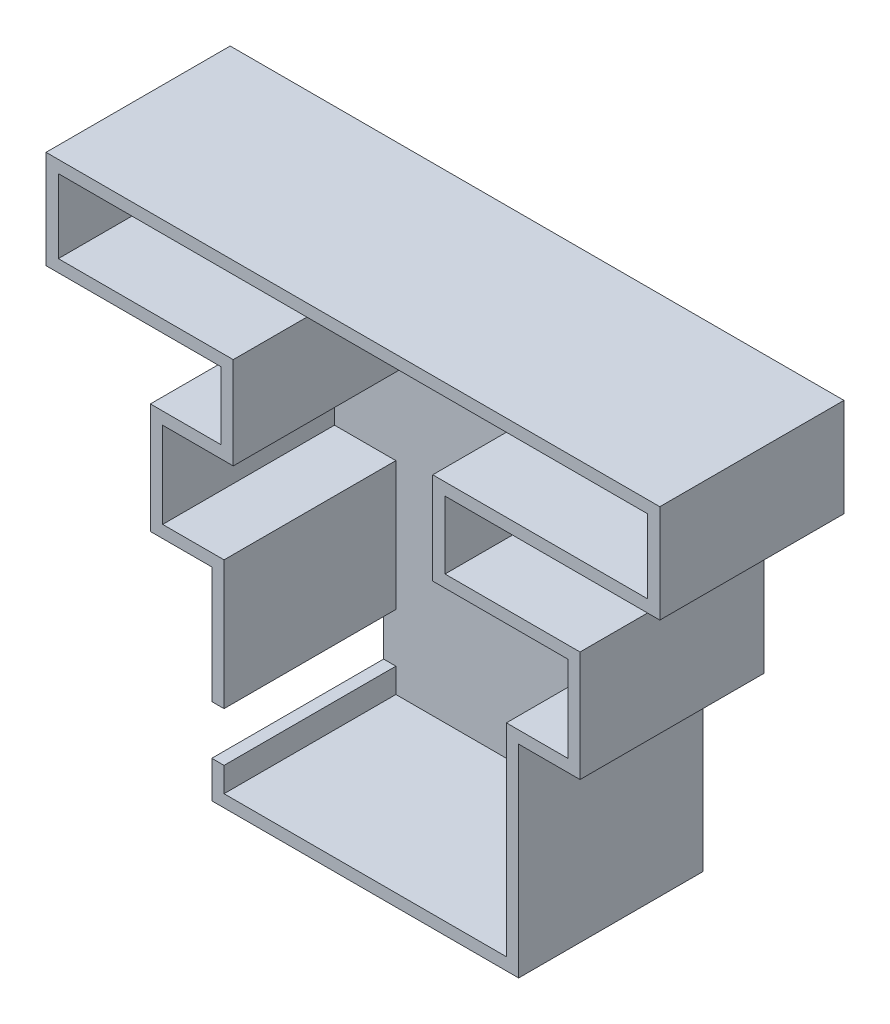
SolidWorks part; units mm, degrees
ref_plane "前视基准面" through (0, 0, 0) normal (0, 0, 1) x (1, 0, 0)
ref_plane "上视基准面" through (0, 0, 0) normal (0, 1, 0) x (1, 0, 0)
ref_plane "右视基准面" through (0, 0, 0) normal (1, 0, 0) x (0, 0, -1)
other "Configuration Table"
sketch "草图3" plane through (0, 0, 0) normal (0, 0, 1) x (1, 0, 0)
  line L0 (-4.5, 23.1299) -> (-4.5, -48.8588) construction
  line L1 (-11.5, 0) -> (11.5, 0)
  line L2 (-11.5, 0) -> (-11.5, -16.5)
  line L3 (-11.5, -16.5) -> (11.5, -16.5)
  line L4 (11.5, 0) -> (11.5, -16.5)
  line L5 (-16.5, 7) -> (16.5, 7)
  line L6 (-16.5, 7) -> (-16.5, 0)
  line L7 (-16.5, 0) -> (16.5, 0)
  line L8 (16.5, 7) -> (16.5, 0)
  line L9 (-10.75, 14.5) -> (5.5, 14.5)
  line L10 (-10.75, 14.5) -> (-10.75, 7)
  line L11 (-10.75, 7) -> (5.5, 7)
  line L12 (5.5, 14.5) -> (5.5, 7)
  line L13 (-26, 21.5) -> (24, 21.5)
  line L14 (-25, 20.5) -> (23, 20.5)
  line L15 (-25, 20.5) -> (-25, 14.5)
  line L16 (-25, 14.5) -> (23, 14.5)
  line L17 (23, 20.5) -> (23, 14.5)
  line L18 (24, 21.5) -> (24, 13.5)
  line L19 (-26, 13.5) -> (-11.75, 13.5)
  line L20 (-26, 21.5) -> (-26, 13.5)
  line L21 (-11.75, 13.5) -> (-11.75, 8)
  line L23 (6.5, 13.5) -> (6.5, 8)
  line L25 (-17.5, 8) -> (-11.75, 8)
  line L26 (17.5, 8) -> (17.5, -1)
  line L27 (-17.5, -1) -> (-12.5, -1)
  line L28 (-17.5, 8) -> (-17.5, -1)
  line L29 (12.5, -1) -> (12.5, -17.5)
  line L30 (-12.5, -17.5) -> (12.5, -17.5)
  line L31 (-12.5, -1) -> (-12.5, -17.5)
  line L33 (-11.75, 15.5) -> (6.5, 15.5) construction
  line L34 (6.5, 15.5) -> (6.5, 6) construction
  line L35 (-11.75, 15.5) -> (-11.75, 6) construction
  line L36 (6.5, 13.5) -> (24, 13.5)
  line L37 (-26, 13.5) -> (24, 13.5) construction
  line L38 (-12.5, 1) -> (12.5, 1) construction
  line L39 (6.5, 8) -> (17.5, 8)
  line L40 (-17.5, 8) -> (17.5, 8) construction
  line L41 (-11.75, 6) -> (6.5, 6) construction
  line L42 (-11.5, 0) -> (11.5, 0) construction
  line L43 (12.5, -1) -> (17.5, -1)
  line L44 (-17.5, -1) -> (17.5, -1) construction
  line L45 (12.5, 1) -> (12.5, -17.5) construction
  line L46 (-12.5, 1) -> (-12.5, -17.5) construction
  dimension "D1" = 23
  dimension "D2" = 16.5
  dimension "D3" = 7
  dimension "D4" = 33
  dimension "D5" = 12
  dimension "D6" = 6.25
  dimension "D7" = 7.5
  dimension "D8" = 10
  dimension "D9" = 48
  dimension "D10" = 20.5
  dimension "D11" = 6
  dimension "D12" = 1
extrude "凸台-拉伸1" add sketch "草图3" along normal blind 15 contours L31 L30 L29 L43 L26 L39 L23 L36 L18 L13 L20 L19 L21 L25 L28 L27
sketch "草图4" plane through (0, 0, 15) normal (0, 0, 1) x (1, 0, 0)
  line L0 (-26, 21.5) -> (-26, 13.5)
  line L1 (-26, 13.5) -> (-11.75, 13.5)
  line L2 (-11.75, 13.5) -> (-11.75, 8)
  line L3 (-11.75, 8) -> (-17.5, 8)
  line L4 (-17.5, 8) -> (-17.5, -1)
  line L5 (-17.5, -1) -> (-12.5, -1)
  line L6 (-12.5, -1) -> (-12.5, -17.5)
  line L7 (-12.5, -17.5) -> (12.5, -17.5)
  line L8 (12.5, -17.5) -> (12.5, -1)
  line L9 (12.5, -1) -> (17.5, -1)
  line L10 (17.5, -1) -> (17.5, 8)
  line L11 (17.5, 8) -> (6.5, 8)
  line L12 (6.5, 8) -> (6.5, 13.5)
  line L13 (6.5, 13.5) -> (24, 13.5)
  line L14 (24, 13.5) -> (24, 21.5)
  line L15 (24, 21.5) -> (-26, 21.5)
  line L16 (23, 20.5) -> (-25, 20.5)
  line L17 (-25, 20.5) -> (-25, 14.5)
  line L18 (-25, 14.5) -> (-10.75, 14.5)
  line L19 (-10.75, 14.5) -> (-10.75, 7)
  line L20 (-10.75, 7) -> (-16.5, 7)
  line L21 (-16.5, 7) -> (-16.5, 0)
  line L22 (-16.5, 0) -> (-11.5, 0)
  line L23 (-11.5, 0) -> (-11.5, -16.5)
  line L24 (-11.5, -16.5) -> (11.5, -16.5)
  line L25 (11.5, -16.5) -> (11.5, 0)
  line L26 (11.5, 0) -> (16.5, 0)
  line L27 (16.5, 0) -> (16.5, 7)
  line L28 (16.5, 7) -> (5.5, 7)
  line L29 (5.5, 7) -> (5.5, 14.5)
  line L30 (5.5, 14.5) -> (23, 14.5)
  line L31 (23, 14.5) -> (23, 20.5)
  dimension "D1" = 1
extrude "切除-拉伸1" cut sketch "草图4" against normal blind 14 contours L16 L17 L18 L19 L20 L21 L22 L23 L24 L25 L26 L27 L28 L29 L30 L31
sketch "草图7" plane through (0, 0, 1) normal (0, 0, 1) x (1, 0, 0)
  line L0 (-25, 20.5) -> (-25, 14.5)
  line L1 (-25, 20.5) -> (-25, 14.5) construction
  line L2 (-25, 14.5) -> (23, 14.5)
  line L3 (23, 14.5) -> (23, 20.5)
  line L4 (23, 20.5) -> (-25, 20.5)
extrude "切除-拉伸2" cut sketch "草图7" against normal up to surface (1 mm away) contours L4 L0 L2 L3 up to face at (-0.9063, 5.625, 0)
sketch "草图8" plane through (-12.5, 0, 0) normal (-1, 0, 0) x (0, 0, 1)
  line L1 (1, -10.5) -> (15, -10.5)
  line L2 (1, -10.5) -> (1, -14.5)
  line L3 (1, -14.5) -> (15, -14.5)
  line L4 (15, -10.5) -> (15, -14.5)
  line L5 (15, -1) -> (15, -17.5) construction
  line L6 (15, -17.5) -> (0, -17.5) construction
  line L7 (0, -1) -> (0, -17.5) construction
  dimension "D1" = 3
  dimension "D2" = 7
  dimension "D3" = 1
extrude "切除-拉伸3" cut sketch "草图8" against normal up to surface (1 mm away) contours L2 L1 L4 L3 up to face at (-11.5, -8.25, 8)
